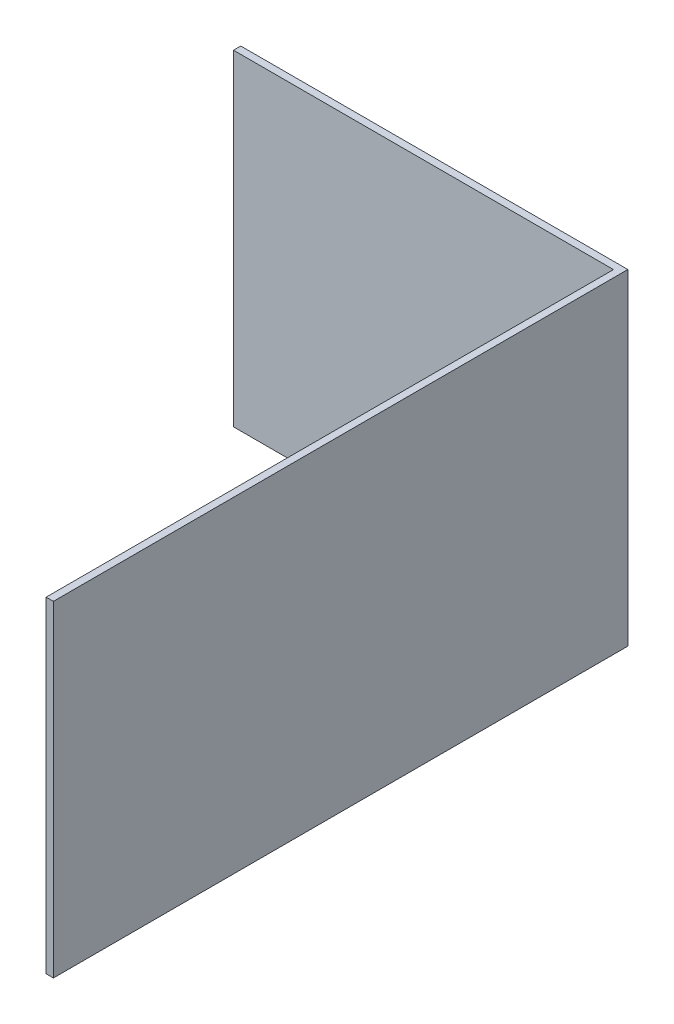
SolidWorks part; units mm, degrees
ref_plane "Front Plane" through (0, 0, 0) normal (0, 0, 1) x (1, 0, 0)
ref_plane "Top Plane" through (0, 0, 0) normal (0, 1, 0) x (1, 0, 0)
ref_plane "Right Plane" through (0, 0, 0) normal (1, 0, 0) x (0, 0, -1)
sketch "Sketch1" plane through (0, 0, 0) normal (0, 1, 0) x (1, 0, 0)
  line L1 (345.3109, -749.2863) -> (345.3109, 423.2106)
  line L2 (345.3109, 423.2106) -> (-440, 423.2106)
  line L3 (345.3109, -749.2863) -> (360.3109, -749.2863)
  line L4 (-440, 423.2106) -> (-440, 438.2106)
  line L5 (-440, 438.2106) -> (360, 438.2106)
  line L6 (360, 438.2106) -> (360.3109, -749.2863)
  dimension "D1" = 15
  dimension "D2" = 15
  dimension "D3" = 0.015
  dimension "D4" = 800
  dimension "D5" = 1187.497
  dimension "D6" = 423.2106
  dimension "D7" = 345.3109
  dimension "D8" = 360.1147
extrude "Boss-Extrude1" add sketch "Sketch1" along normal blind 674.1356
